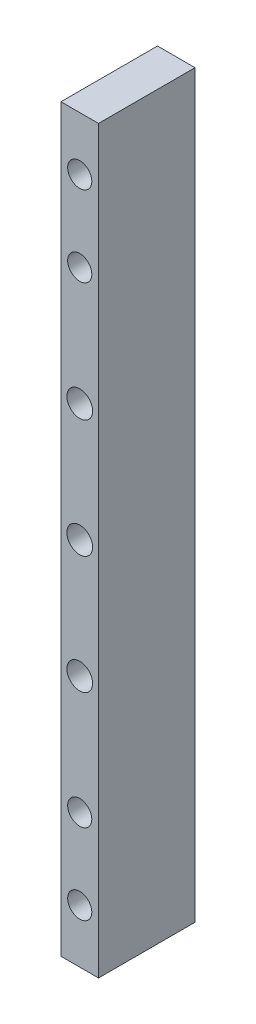
SolidWorks part; units mm, degrees
material "ABS"
ref_plane "正面" through (0, 0, 0) normal (0, 0, 1) x (1, 0, 0)
ref_plane "平面" through (0, 0, 0) normal (0, 1, 0) x (1, 0, 0)
ref_plane "右側面" through (0, 0, 0) normal (1, 0, 0) x (0, 0, -1)
sketch "ｽｹｯﾁ1" plane through (0, 0, 0) normal (0, 0, 1) x (1, 0, 0)
  line L1 (-3.5, 69) -> (3.5, 69)
  line L2 (-3.5, 69) -> (-3.5, -69)
  line L3 (-3.5, -69) -> (3.5, -69)
  line L4 (3.5, 69) -> (3.5, -69)
  line L5 (-3.5, 69) -> (3.5, -69) construction
  line L6 (-3.5, -69) -> (3.5, 69) construction
  point P0 (0, 0)
  dimension "D1" = 7
  dimension "D2" = 138
extrude "ﾎﾞｽ - 押し出し1" add sketch "ｽｹｯﾁ1" along normal blind 18
hole_wizard "M4 すきま穴1" positions "ｽｹｯﾁ2" profile "ｽｹｯﾁ3" hole size "M4" standard "JIS" end condition through all
sketch "ｽｹｯﾁ2" plane through (0, 0, 18) normal (0, 0, 1) x (1, 0, 0)
  line L0 (-3.5, 0) -> (3.5, 0) construction
  line L1 (-3.5, 69) -> (-3.5, -69) construction
  line L2 (3.5, -69) -> (3.5, 69) construction
  point P0 (0, 0)
  point P13 (0, 22)
  point P15 (0, -22)
  dimension "D1" = 44
sketch "ｽｹｯﾁ3" plane through (0, 0, 18) normal (1, 0, 0) x (0, -1, 0)
  line L0 (0, 0) -> (0, 18)
  line L1 (0, 18) -> (2.4, 18)
  line L2 (2.4, 18) -> (2.4, 0)
  line L5 (2.4, 0) -> (0, 0)
  line L11 (0, -6.35) -> (0, 107.95) construction
  dimension "通し穴の直径" = 4.8
  dimension "通し穴の深さ" = 18
sketch "ｽｹｯﾁ4" plane through (0, 0, 18) normal (0, 0, 1) x (1, 0, 0)
  line L0 (0, 69) -> (0, -69) construction
  line L1 (3.5, 69) -> (-3.5, 69) construction
  line L2 (-3.5, -69) -> (3.5, -69) construction
  point P6 (0, 59)
  point P7 (0, 44)
  dimension "D1" = 10
  dimension "D2" = 15
hole_wizard "M4 すきま穴2" positions "3Dｽｹｯﾁ1" profile "ｽｹｯﾁ5" hole size "M4" standard "JIS" end condition through all
sketch3d "3Dｽｹｯﾁ1"
  point P1 (0, 44, 18)
  point P4 (0, 59, 18)
sketch "ｽｹｯﾁ5" plane through (0, 44, 18) normal (1, 0, 0) x (0, -1, 0)
  line L0 (0, 0) -> (0, 18)
  line L1 (0, 18) -> (2.25, 18)
  line L2 (2.25, 18) -> (2.25, 0)
  line L5 (2.25, 0) -> (0, 0)
  line L11 (0, -6.35) -> (0, 107.95) construction
  dimension "通し穴の直径" = 4.5
  dimension "通し穴の深さ" = 18
mirror "ﾐﾗｰ1" about plane through (0, 0, 0) normal (0, 1, 0) of "M4 すきま穴2"
